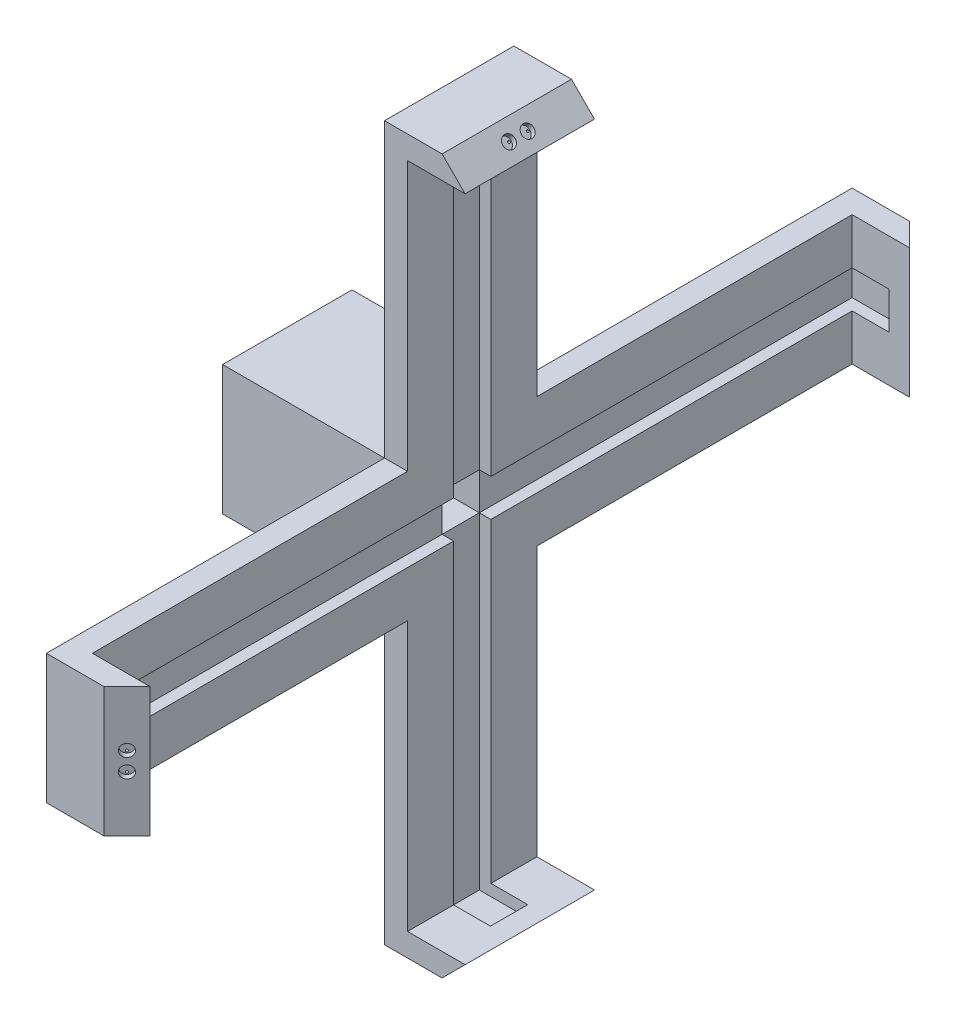
SolidWorks part; units mm, degrees
ref_plane "Front Plane" through (0, 0, 0) normal (0, 0, 1) x (1, 0, 0)
ref_plane "Top Plane" through (0, 0, 0) normal (0, 1, 0) x (1, 0, 0)
ref_plane "Right Plane" through (0, 0, 0) normal (1, 0, 0) x (0, 0, -1)
sketch "Sketch1" plane through (0, 0, 0) normal (0, 0, 1) x (1, 0, 0)
  circle A0 centre (0, 0) radius 28.1
extrude "Boss-Extrude2" add sketch "Sketch1" along normal blind 24
sketch "Sketch3" plane through (0, 0, 0) normal (0, 0, -1) x (-1, 0, 0)
  line L2 (-1.6618, 2.5) -> (1.6618, 2.5)
  arc A1 (-1.6618, 2.5) -> (1.6618, 2.5) centre (0, 0) ccw
extrude "Cut-Extrude2" cut sketch "Sketch3" against normal blind 21.5
sketch "Sketch4" plane through (0, 0, 0) normal (0, 0, -1) x (-1, 0, 0)
  circle A0 centre (0, 0) radius 3
extrude "Cut-Extrude3" cut sketch "Sketch4" against normal blind 9.5
sketch "Sketch6" plane through (0, 0, 0) normal (0, 0, -1) x (-1, 0, 0)
  circle A0 centre (0, 0) radius 6.025
extrude "Cut-Extrude4" cut sketch "Sketch6" against normal blind 6.2
sketch "Sketch7" plane through (0, 0, 24) normal (0, 0, 1) x (1, 0, 0)
  line L1 (-28.1, -28.1) -> (28.1, -28.1)
  line L2 (-28.1, -28.1) -> (-28.1, 28.1)
  line L3 (-28.1, 28.1) -> (28.1, 28.1)
  line L4 (28.1, -28.1) -> (28.1, 28.1)
  line L5 (-28.1, -28.1) -> (28.1, 28.1) construction
  line L6 (-28.1, 28.1) -> (28.1, -28.1) construction
  point P0 (0, 0)
extrude "Boss-Extrude3" add sketch "Sketch7" along normal blind 56.2
sketch "Sketch8" plane through (28.1, 0, 0) normal (1, 0, 0) x (0, 0, -1)
  line L0 (-80.2, 28.1) -> (-24, 28.1) construction
  line L1 (-80.2, 28.1) -> (-24, 28.1)
  line L2 (-80.2, 28.1) -> (-80.2, -28.1)
  line L3 (-80.2, -28.1) -> (-24, -28.1)
  line L4 (-24, 28.1) -> (-24, -28.1)
  line L5 (-80.2, -28.1) -> (-80.2, 28.1) construction
extrude "Boss-Extrude4" add sketch "Sketch8" along normal blind 14.14
sketch "Sketch10" plane through (42.24, 0, 0) normal (1, 0, 0) x (0, 0, -1)
  line L1 (-80.2, 28.1) -> (-24, 28.1)
  line L2 (-80.2, 28.1) -> (-80.2, -28.1)
  line L3 (-80.2, -28.1) -> (-24, -28.1)
  line L4 (-24, 28.1) -> (-24, -28.1)
extrude "Boss-Extrude5" add sketch "Sketch10" along normal blind 10
sketch "Sketch11" plane through (0, 0, 80.2) normal (0, 0, 1) x (1, 0, 0)
  line L1 (52.24, 28.1) -> (-28.1, 28.1) construction
  line L3 (42.24, 28.1) -> (52.24, 28.1)
  line L4 (42.24, 28.1) -> (42.24, -28.1)
  line L5 (42.24, -28.1) -> (52.24, -28.1)
  line L6 (52.24, 28.1) -> (52.24, -28.1)
extrude "Boss-Extrude6" add sketch "Sketch11" along normal blind 146.9
sketch "Sketch12" plane through (0, 28.1, 0) normal (0, 1, 0) x (1, 0, 0)
  line L1 (42.24, -80.2) -> (52.24, -80.2)
  line L2 (42.24, -80.2) -> (42.24, -24)
  line L3 (42.24, -24) -> (52.24, -24)
  line L4 (52.24, -80.2) -> (52.24, -24)
extrude "Boss-Extrude7" add sketch "Sketch12" along normal blind 126.9
sketch "Sketch13" plane through (0, 0, 24) normal (0, 0, -1) x (-1, 0, 0)
  line L1 (-52.24, -28.1) -> (-42.24, -28.1)
  line L2 (-52.24, -28.1) -> (-52.24, 28.1)
  line L3 (-52.24, 28.1) -> (-42.24, 28.1)
  line L4 (-42.24, -28.1) -> (-42.24, 28.1)
extrude "Boss-Extrude8" add sketch "Sketch13" along normal blind 146.9
sketch "Sketch14" plane through (0, -28.1, 0) normal (0, -1, 0) x (-1, 0, 0)
  line L0 (-52.24, -227.1) -> (-52.24, 122.9) construction
  line L1 (-42.24, -24) -> (-52.24, -24)
  line L2 (-42.24, -24) -> (-42.24, -80.2)
  line L3 (-42.24, -80.2) -> (-52.24, -80.2)
  line L4 (-52.24, -24) -> (-52.24, -80.2)
extrude "Boss-Extrude9" add sketch "Sketch14" along normal blind 126.9
sketch "Sketch15" plane through (52.24, 0, 0) normal (1, 0, 0) x (0, 0, -1)
  line L1 (-80.2, 28.1) -> (-227.1, 28.1) construction
  line L3 (-217.1, 28.1) -> (-227.1, 28.1)
  line L4 (-217.1, 28.1) -> (-217.1, -28.1)
  line L5 (-217.1, -28.1) -> (-227.1, -28.1)
  line L6 (-227.1, 28.1) -> (-227.1, -28.1)
extrude "Boss-Extrude10" add sketch "Sketch15" along normal blind 25
sketch "Sketch16" plane through (52.24, 0, 0) normal (1, 0, 0) x (0, 0, -1)
  line L1 (122.9, 28.1) -> (-24, 28.1) construction
  line L3 (112.9, 28.1) -> (122.9, 28.1)
  line L4 (112.9, 28.1) -> (112.9, -28.1)
  line L5 (112.9, -28.1) -> (122.9, -28.1)
  line L6 (122.9, 28.1) -> (122.9, -28.1)
extrude "Boss-Extrude11" add sketch "Sketch16" along normal blind 25
sketch "Sketch17" plane through (52.24, 0, 0) normal (1, 0, 0) x (0, 0, -1)
  line L1 (-80.2, 155) -> (-80.2, 28.1) construction
  line L3 (-80.2, 145) -> (-24, 145)
  line L4 (-80.2, 145) -> (-80.2, 155)
  line L5 (-80.2, 155) -> (-24, 155)
  line L6 (-24, 145) -> (-24, 155)
extrude "Boss-Extrude12" add sketch "Sketch17" along normal blind 25
sketch "Sketch18" plane through (52.24, 0, 0) normal (1, 0, 0) x (0, 0, -1)
  line L1 (-80.2, -155) -> (-80.2, -28.1) construction
  line L3 (-80.2, -145) -> (-24, -145)
  line L4 (-80.2, -145) -> (-80.2, -155)
  line L5 (-80.2, -155) -> (-24, -155)
  line L6 (-24, -145) -> (-24, -155)
extrude "Boss-Extrude13" add sketch "Sketch18" along normal blind 25
sketch "Sketch19" plane through (-28.1, 0, 0) normal (-1, 0, 0) x (0, 0, 1)
  line L7 (26.5, 25.6) -> (77.7, 25.6)
  line L8 (26.5, 25.6) -> (26.5, -25.6)
  line L9 (26.5, -25.6) -> (77.7, -25.6)
  line L10 (77.7, 25.6) -> (77.7, -25.6)
extrude "Cut-Extrude5" cut sketch "Sketch19" against normal blind 63.7
sketch "Sketch20" plane through (0, 0, 0) normal (0, 0, -1) x (-1, 0, 0)
  arc A1 (0, 15) -> (-15, 0) centre (0, 0) ccw
sketch3d "3DSketch2"
  line L2 (0, 15, 0) -> (0, 22.5, 0)
  line L3 (0, 15, 0) -> (0, 15, 42.1431)
  line L4 (0, 15, 42.1431) -> (0, 22.5, 42.1431)
  line L5 (0, 22.5, 0) -> (0, 22.5, 42.1431)
  arc A0 (0, 15, 0) -> (15, 0, 0) centre (0, 0, 0) ccw construction
  point P10 (0, 0, -15)
sweep "Cut-Sweep2" cut profiles "3DSketch2" path "Sketch20"
sketch "Sketch23" plane through (52.24, 0, 0) normal (1, 0, 0) x (0, 0, -1)
  line L1 (-217.1, -28.1) -> (-217.1, 28.1) construction
  line L3 (112.9, 28.1) -> (112.9, -28.1) construction
  line L4 (-217.1, 8.1) -> (112.9, 8.1)
  line L5 (-217.1, 8.1) -> (-217.1, -8.1)
  line L6 (-217.1, -8.1) -> (112.9, -8.1)
  line L7 (112.9, 8.1) -> (112.9, -8.1)
extrude "Cut-Extrude7" cut sketch "Sketch23" against normal blind 5
sketch "Sketch24" plane through (52.24, 0, 0) normal (1, 0, 0) x (0, 0, -1)
  line L1 (-80.2, 145) -> (-24, 145) construction
  line L3 (-24, -145) -> (-80.2, -145) construction
  line L4 (-60.2, 145) -> (-44, 145)
  line L5 (-60.2, 145) -> (-60.2, -145)
  line L6 (-60.2, -145) -> (-44, -145)
  line L7 (-44, 145) -> (-44, -145)
extrude "Cut-Extrude8" cut sketch "Sketch24" against normal blind 5
sketch "Sketch25" plane through (47.24, 0, 0) normal (1, 0, 0) x (0, 0, -1)
  line L1 (-60.2, 8.1) -> (-44, 8.1)
  line L2 (-60.2, 8.1) -> (-60.2, -8.1)
  line L3 (-60.2, -8.1) -> (-44, -8.1)
  line L4 (-44, 8.1) -> (-44, -8.1)
extrude "Cut-Extrude12" cut sketch "Sketch25" against normal blind 25
sketch "Sketch26" plane through (0, -28.1, 0) normal (0, -1, 0) x (-1, 0, 0)
  line L0 (-77.24, -217.1) -> (-67.24, -227.1)
  line L1 (-42.24, -227.1) -> (-77.24, -227.1) construction
  line L2 (-77.24, 112.9) -> (-67.24, 122.9)
  line L3 (-77.24, 112.9) -> (-77.24, 122.9) construction
  line L4 (-77.24, 122.9) -> (-42.24, 122.9) construction
  line L5 (-67.24, -227.1) -> (-77.24, -227.1)
  line L6 (-77.24, -227.1) -> (-77.24, -217.1)
  line L7 (-77.24, 112.9) -> (-77.24, 122.9)
  line L8 (-77.24, 122.9) -> (-67.24, 122.9)
extrude "Cut-Extrude13" cut sketch "Sketch26" against normal blind 56.2
sketch "Sketch27" plane through (0, 0, 80.2) normal (0, 0, 1) x (1, 0, 0)
  line L0 (77.24, -145) -> (67.24, -155)
  line L1 (77.24, -155) -> (42.24, -155) construction
  line L2 (67.24, -155) -> (77.24, -155)
  line L3 (77.24, -155) -> (77.24, -145)
  line L4 (77.24, 145) -> (67.24, 155)
  line L5 (42.24, 155) -> (77.24, 155) construction
  line L6 (77.24, 155) -> (67.24, 155)
  line L7 (77.24, 155) -> (77.24, 145)
extrude "Cut-Extrude14" cut sketch "Sketch27" against normal blind 56.2
sketch "Sketch28" plane through (0, -145, 0) normal (0, 1, 0) x (1, 0, 0)
  line L1 (47.24, -44) -> (68.24, -44)
  line L2 (47.24, -44) -> (47.24, -60.2)
  line L3 (47.24, -60.2) -> (68.24, -60.2)
  line L4 (68.24, -44) -> (68.24, -60.2)
extrude "Cut-Extrude15" cut sketch "Sketch28" against normal blind 5
sketch "Sketch29" plane through (0, 145, 0) normal (0, -1, 0) x (-1, 0, 0)
  line L1 (-47.24, -60.2) -> (-68.24, -60.2)
  line L2 (-47.24, -60.2) -> (-47.24, -44)
  line L3 (-47.24, -44) -> (-68.24, -44)
  line L4 (-68.24, -60.2) -> (-68.24, -44)
extrude "Cut-Extrude16" cut sketch "Sketch29" against normal blind 5
sketch "Sketch30" plane through (0, 0, 217.1) normal (0, 0, -1) x (-1, 0, 0)
  line L1 (-47.24, -8.1) -> (-68.24, -8.1)
  line L2 (-47.24, -8.1) -> (-47.24, 8.1)
  line L3 (-47.24, 8.1) -> (-68.24, 8.1)
  line L4 (-68.24, -8.1) -> (-68.24, 8.1)
extrude "Cut-Extrude17" cut sketch "Sketch30" against normal blind 5
sketch "Sketch31" plane through (0, 0, -112.9) normal (0, 0, 1) x (1, 0, 0)
  line L1 (47.24, 8.1) -> (68.24, 8.1)
  line L2 (47.24, 8.1) -> (47.24, -8.1)
  line L3 (47.24, -8.1) -> (68.24, -8.1)
  line L4 (68.24, 8.1) -> (68.24, -8.1)
extrude "Cut-Extrude18" cut sketch "Sketch31" against normal blind 5
sketch "Sketch33" plane through (147.17, 0, 147.17) normal (0.7071, 0, 0.7071) x (0.7071, 0, -0.7071)
  circle A0 centre (-105.967, 4.05) radius 2.65
  circle A1 centre (-105.967, -4.05) radius 2.65
extrude "Cut-Extrude19" cut sketch "Sketch33" against normal blind 2.4
sketch "Sketch34" plane through (145.4729, 0, 145.4729) normal (0.7071, 0, 0.7071) x (0.7071, 0, -0.7071)
  circle A2 centre (-105.967, 5.75) radius 0.5
  circle A3 centre (-105.967, 2.35) radius 0.5
  circle A4 centre (-105.967, -2.35) radius 0.5
  circle A5 centre (-105.967, -5.75) radius 0.5
extrude "Cut-Extrude20" cut sketch "Sketch34" against normal blind 10
sketch "Sketch35" plane through (95.07, 0, -95.07) normal (0.7071, 0, -0.7071) x (-0.7071, 0, -0.7071)
  circle A0 centre (32.2865, -4.05) radius 2.65
  circle A1 centre (32.2865, 4.05) radius 2.65
extrude "Cut-Extrude21" cut sketch "Sketch35" against normal blind 2.4
sketch "Sketch36" plane through (93.3729, 0, -93.3729) normal (0.7071, 0, -0.7071) x (-0.7071, 0, -0.7071)
  circle A2 centre (32.2865, -5.75) radius 0.5
  circle A3 centre (32.2865, -2.35) radius 0.5
  circle A5 centre (32.2865, 2.35) radius 0.5
  circle A6 centre (32.2865, 5.75) radius 0.5
extrude "Cut-Extrude22" cut sketch "Sketch36" against normal blind 10
sketch "Sketch37" plane through (111.12, -111.12, 0) normal (0.7071, -0.7071, 0) x (0, 0, -1)
  circle A0 centre (-56.15, -54.9846) radius 2.65
  circle A1 centre (-48.05, -54.9846) radius 2.65
extrude "Cut-Extrude23" cut sketch "Sketch37" against normal blind 2.4
sketch "Sketch38" plane through (109.4229, -109.4229, 0) normal (0.7071, -0.7071, 0) x (0, 0, -1)
  circle A2 centre (-57.85, -54.9846) radius 0.5
  circle A3 centre (-54.45, -54.9846) radius 0.5
  circle A4 centre (-49.75, -54.9846) radius 0.5
  circle A5 centre (-46.35, -54.9846) radius 0.5
extrude "Cut-Extrude24" cut sketch "Sketch38" against normal blind 10
sketch "Sketch39" plane through (111.12, 111.12, 0) normal (0.7071, 0.7071, 0) x (0.7071, -0.7071, 0)
  circle A0 centre (-54.9846, -48.05) radius 2.65
  circle A1 centre (-54.9846, -56.15) radius 2.65
extrude "Cut-Extrude25" cut sketch "Sketch39" against normal blind 2.4
sketch "Sketch40" plane through (109.4229, 109.4229, 0) normal (0.7071, 0.7071, 0) x (0.7071, -0.7071, 0)
  circle A2 centre (-54.9846, -46.35) radius 0.5
  circle A3 centre (-54.9846, -49.75) radius 0.5
  circle A4 centre (-54.9846, -54.45) radius 0.5
  circle A5 centre (-54.9846, -57.85) radius 0.5
extrude "Cut-Extrude26" cut sketch "Sketch40" against normal blind 10
sketch "Sketch41" plane through (0, 0, 0) normal (0, 0, -1) x (-1, 0, 0)
  circle A0 centre (0, 18.75) radius 3.75
  circle A1 centre (-18.75, 0) radius 3.75
extrude "Cut-Extrude28" cut sketch "Sketch41" against normal blind 30
sketch "Sketch43" plane through (0, 0, 24) normal (0, 0, -1) x (-1, 0, 0)
  line L0 (-52.24, -145) -> (-42.24, -145)
  line L1 (-42.24, -155) -> (-42.24, -28.1) construction
